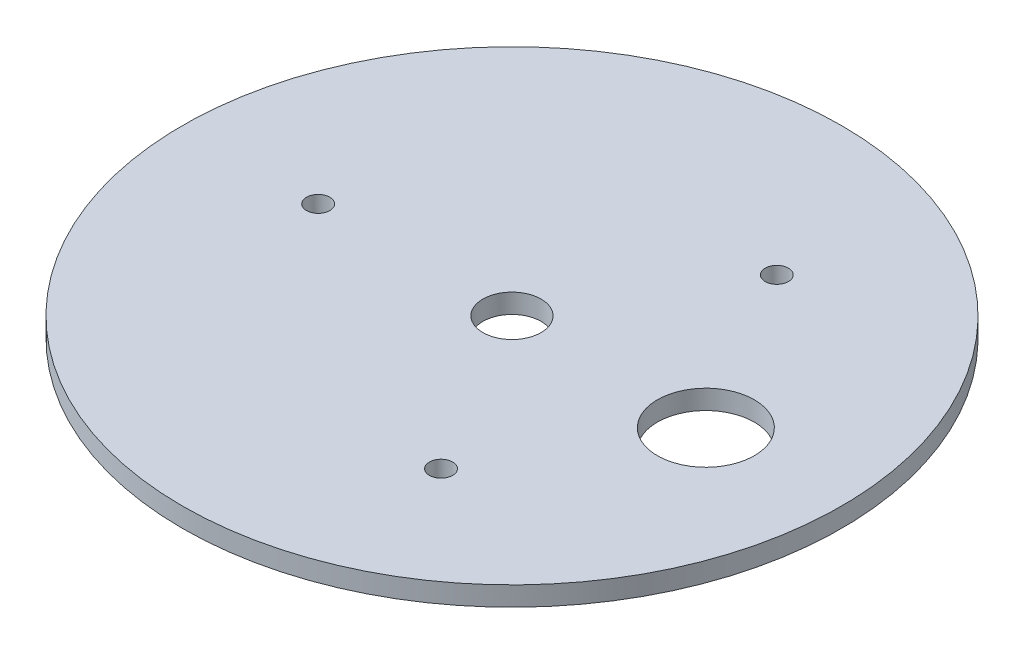
SolidWorks part; units mm, degrees
material "普通碳钢"
ref_plane "前视基准面" through (0, 0, 0) normal (0, 0, 1) x (1, 0, 0)
ref_plane "上视基准面" through (0, 0, 0) normal (0, 1, 0) x (1, 0, 0)
ref_plane "右视基准面" through (0, 0, 0) normal (1, 0, 0) x (0, 0, -1)
sketch "草图1" plane through (0, 0, 0) normal (0, 0, 1) x (1, 0, 0)
  line L0 (0, 0) -> (0, 5)
  line L1 (0, 0) -> (-85, 0)
  line L2 (-85, 0) -> (-85, 5)
  line L3 (-85, 5) -> (0, 5)
  dimension "D1" = 85
  dimension "D3" = 5
revolve "旋转1" add sketch "草图1" angle 360 about L0
sketch "草图2" plane through (0, 0, 0) normal (0, 1, 0) x (1, 0, 0)
  line L0 (0, 0) -> (50, 0) construction
  circle A0 centre (50, 0) radius 12.5
  circle A1 centre (0, 0) radius 50 construction
  circle A2 centre (0, 0) radius 7.5
  circle A4 centre (-50, 0) radius 3
  circle A5 centre (25, 43.3013) radius 3
  circle A6 centre (25, -43.3013) radius 3
  point P15 (0, 0)
  dimension "D3" = 25
  dimension "D4" = 3
  dimension "D1" = 100
  dimension "D2" = 15
  dimension "D5" = 6
extrude "切除-拉伸1" cut sketch "草图2" along normal blind 20
